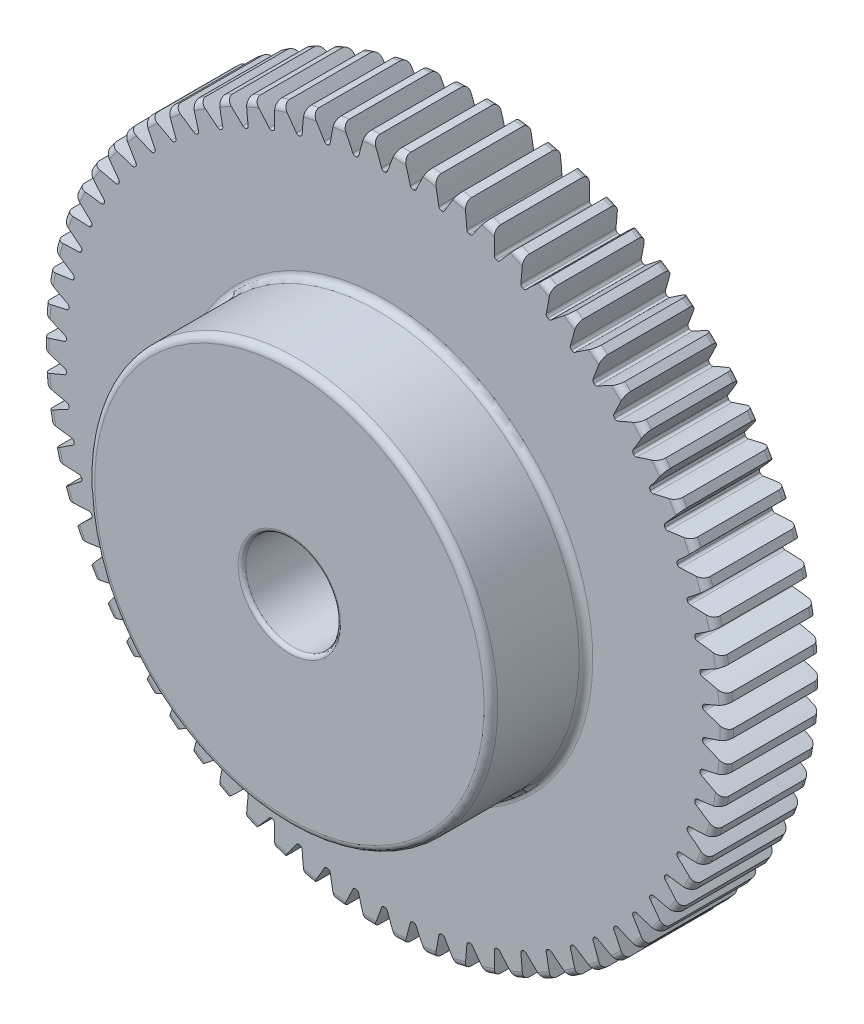
SolidWorks part; units mm, degrees
material "AISI 1020"
ref_plane "Front Plane" through (0, 0, 0) normal (0, 0, 1) x (1, 0, 0)
ref_plane "Top Plane" through (0, 0, 0) normal (0, 1, 0) x (1, 0, 0)
ref_plane "Right Plane" through (0, 0, 0) normal (1, 0, 0) x (0, 0, -1)
sketch "Sketch1" plane through (0, 0, 0) normal (0, 0, 1) x (1, 0, 0)
  line L0 (-889, 0) -> (889, 0) construction
  circle A0 centre (0, 0) radius 45.72 construction
  circle A1 centre (0, 0) radius 44.45 construction
  circle A2 centre (0, 0) radius 42.545 construction
  circle A3 centre (0, 0) radius 26.924 construction
  circle A4 centre (0, 0) radius 6.35 construction
  dimension "D2" = 1.27
  dimension "D3" = 3.175
  dimension "D1" = 3.175
sketch "Sketch2" plane through (0, 0, 0) normal (1, 0, 0) x (0, 0, -1)
  line L0 (0, 0) -> (-12.7, 0) construction
  line L1 (-12.7, 0) -> (-25.4, 0) construction
  dimension "Overall Width" = 25.4
  dimension "Face Width" = 12.7
sketch "Sketch4" plane through (0, 0, 0) normal (1, 0, 0) x (0, 0, -1)
  line L0 (-25.4, 6.35) -> (-25.4, 26.924)
  line L1 (-25.4, 26.924) -> (-12.7, 26.924)
  line L2 (-12.7, 26.924) -> (-12.7, 45.72)
  line L3 (-12.7, 45.72) -> (0, 45.72)
  line L4 (0, 45.72) -> (0, 6.35)
  line L5 (-12.7, 26.924) -> (-12.7, 0) construction
  line L6 (0, 45.72) -> (0, -45.72) construction
  line L7 (-12.7, 26.924) -> (0, 26.924) construction
  line L12 (-25.4, 6.35) -> (0, 6.35)
revolve "Revolve1" add sketch "Sketch4" angle 360 about L1
fillet "Fillet2" radius 0.9144 4 edges at (0, 26.924, 25.4) (0, 26.924, 12.7) (0, 45.72, 12.7) (0, 45.72, 0)
sketch "Sketch7" plane through (0, 0, 12.7) normal (0, 0, 1) x (1, 0, 0)
  line L0 (0, 0) -> (0, 45.72) construction
  line L1 (0.9974, 44.4388) -> (1.4871, 45.6958) construction
  line L3 (2.0512, 45.674) -> (1.9942, 44.4052) construction
  line L4 (1.9942, 44.4052) -> (1.9088, 42.5022) construction
  line L5 (0, 0) -> (1.9088, 42.5022) construction
  line L6 (0.9974, 44.4388) -> (0, 0) construction
  line L7 (0.9974, 44.4388) -> (1.0259, 45.7085) construction
  line L8 (0.9974, 44.4388) -> (0, 0) construction
  circle A0 centre (0, 0) radius 45.72 construction
  arc A1 (-0.0358, 42.545) -> (0.0358, 42.545) centre (0, 0) cw
  circle A2 centre (0, 0) radius 42.545 construction
  arc A3 (-0.9974, 44.4388) -> (0.9974, 44.4388) centre (0, 0) cw construction
  circle A4 centre (0, 0) radius 44.45 construction
  arc A5 (2.5931, 45.6464) -> (1.509, 45.6951) centre (0, 0) ccw construction
  arc A6 (0.9974, 44.4388) -> (2.9901, 44.3493) centre (0, 0) cw construction
  arc A7 (-1.509, 45.6951) -> (1.509, 45.6951) centre (0, 0) cw
  arc A8 (0.3963, 42.8017) -> (1.509, 45.6951) centre (42.4151, 28.3026) cw
  arc A9 (-0.3963, 42.8017) -> (-1.509, 45.6951) centre (-42.4151, 28.3026) ccw
  arc A10 (-0.0358, 42.545) -> (-0.3963, 42.8017) centre (-0.0361, 42.926) cw
  arc A11 (0.0358, 42.545) -> (0.3963, 42.8017) centre (0.0361, 42.926) ccw
  point P26 (-0.3082, 42.5439)
  point P29 (0.3082, 42.5439)
  dimension "D4" = 0.381
  dimension "D5" = 44.45
  dimension "D3" = 20
  dimension "D1" = 3.9898
  dimension "D2" = 1.9949
extrude "Cut-Extrude2" cut sketch "Sketch7" against normal through all
pattern_circular "CirPattern1" count 70 over 360 about axis through (0, 0, 0) along (0, 0, 1) of "Cut-Extrude2"
fillet "Fillet3" radius 0.508 2 edges at (0, 6.35, 0) (0, 6.35, 25.4)
equation "\"D1@Sketch1\"=2.5*(\"Pitch Dia.@Sketch1\"/\"Number of Teeth@Sketch1\")"
equation "\"D1@CirPattern1\"=\"Number of Teeth@Sketch1\""
equation "\"D1@Fillet2\"=\"OD@Sketch1\"*.01"
equation "\"D1@Sketch7\"=3.14159*(\"Pitch Dia.@Sketch1\"/\"Number of Teeth@Sketch1\")"
equation "\"D2@Sketch7\"=\"D1@Sketch7\"/2"
equation "\"D4@Sketch7\"=\"D1@Sketch7\"*.0955"
equation "\"D5@Sketch7\"=\"Pitch Dia.@Sketch1\"/2"
